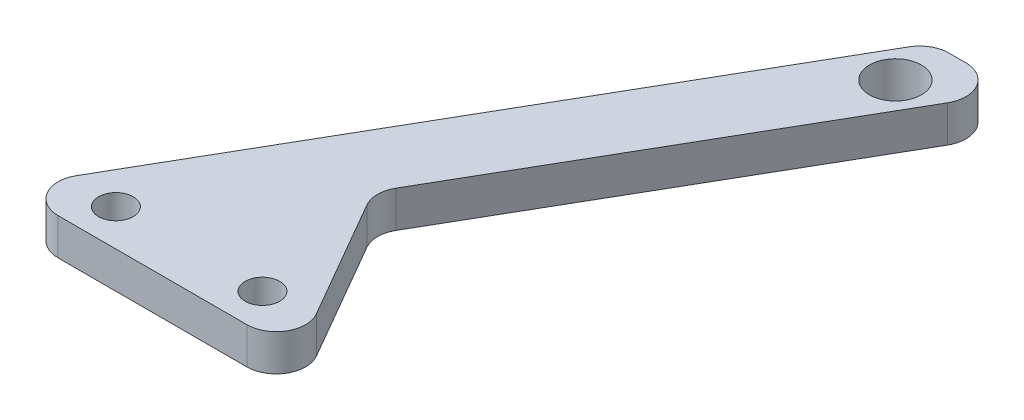
SolidWorks part; units mm, degrees
material "UHMW"
ref_plane "Front Plane" through (0, 0, 0) normal (0, 0, 1) x (1, 0, 0)
ref_plane "Top Plane" through (0, 0, 0) normal (0, 1, 0) x (1, 0, 0)
ref_plane "Right Plane" through (0, 0, 0) normal (1, 0, 0) x (0, 0, -1)
sketch "Sketch1" plane through (0, 0, 0) normal (0, 1, 0) x (1, 0, 0)
  line L0 (14.6647, 25.4) -> (-14.6647, -25.4)
  line L1 (-14.6647, -25.4) -> (10.5003, -25.4)
  line L2 (10.5003, -25.4) -> (1.584, -9.9565)
  line L4 (14.6647, 25.4) -> (21.997, 25.4)
  line L5 (21.997, 25.4) -> (1.584, -9.9565)
  line L6 (-8.4322, -22.225) -> (4.2678, -22.225) construction
  circle A0 centre (-8.4322, -22.225) radius 1.5
  circle A1 centre (4.2678, -22.225) radius 1.5
  point P0 (-2.0822, -22.225)
  point P9 (-2.0822, -25.4)
  point P14 (18.3309, 25.4)
  dimension "D2" = 3
  dimension "D5" = 3.175
  dimension "D1" = 12.7
  dimension "D3" = 60
  dimension "D4" = 60
  dimension "D6" = 6.35
  dimension "D7" = 3.81
  dimension "D8" = 25.4
  dimension "D9" = 50.8
extrude "Boss-Extrude1" add sketch "Sketch1" along normal blind 3.175
sketch "Sketch2" plane through (0, 3.175, 0) normal (0, 1, 0) x (1, 0, 0)
  line L0 (13.0772, 22.6504) -> (18.5765, 19.4754) construction
  line L1 (14.6647, 25.4) -> (-14.6647, -25.4) construction
  line L2 (1.584, -9.9565) -> (21.997, 25.4) construction
  circle A0 centre (15.8268, 21.0629) radius 2.2479
  dimension "D1" = 4.4958
  dimension "D2" = 3.175
extrude "Cut-Extrude1" cut sketch "Sketch2" against normal through all
fillet "Fillet1" radius 2.54 5 edges at (14.6647, 1.5875, -25.4) (21.997, 1.5875, -25.4) (-14.6647, 1.5875, 25.4) (1.584, 1.5875, 9.9565) (10.5003, 1.5875, 25.4)
